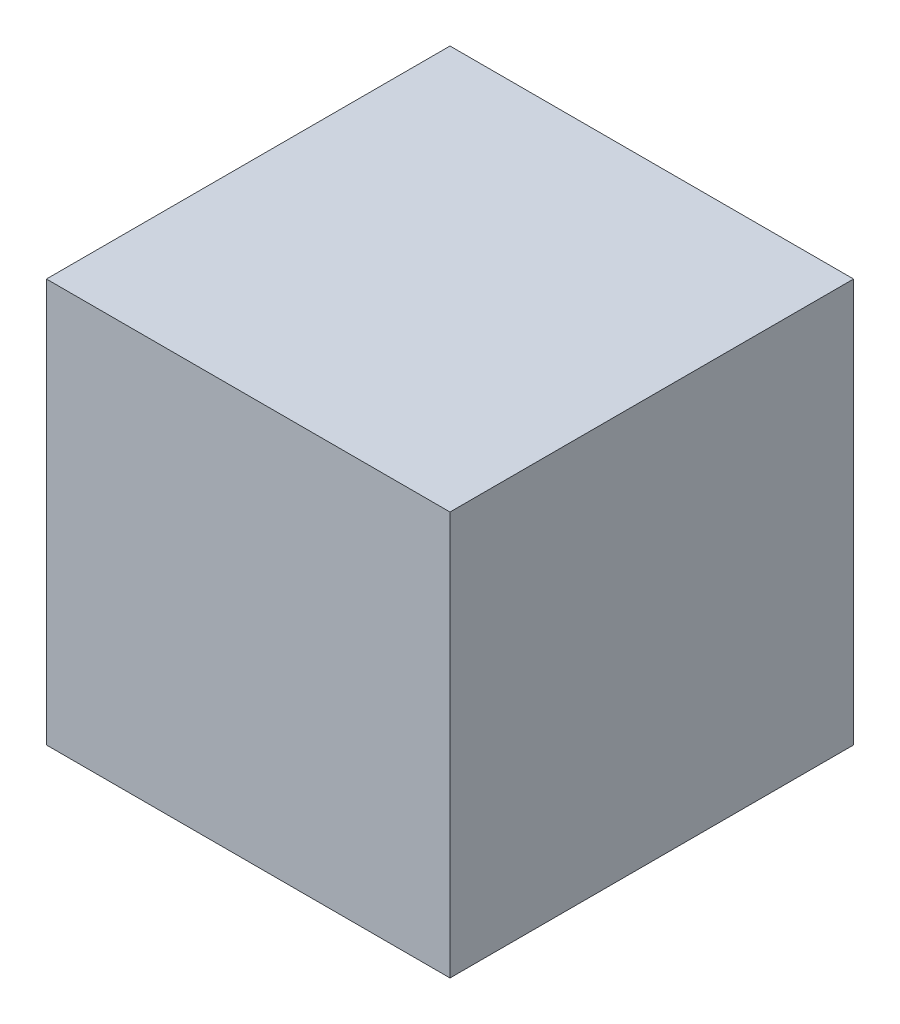
SolidWorks part; units mm, degrees
ref_plane "前视基准面" through (0, 0, 0) normal (0, 0, 1) x (1, 0, 0)
ref_plane "上视基准面" through (0, 0, 0) normal (0, 1, 0) x (1, 0, 0)
ref_plane "右视基准面" through (0, 0, 0) normal (1, 0, 0) x (0, 0, -1)
sketch "草图1" plane through (0, 0, 0) normal (0, 0, 1) x (1, 0, 0)
  line L1 (-50, -50) -> (50, -50)
  line L2 (-50, -50) -> (-50, 50)
  line L3 (-50, 50) -> (50, 50)
  line L4 (50, -50) -> (50, 50)
  line L5 (-50, -50) -> (50, 50) construction
  line L6 (-50, 50) -> (50, -50) construction
  point P0 (0, 0)
  dimension "D1" = 100
  dimension "D2" = 100
extrude "凸台-拉伸1" add sketch "草图1" along normal mid plane 100
